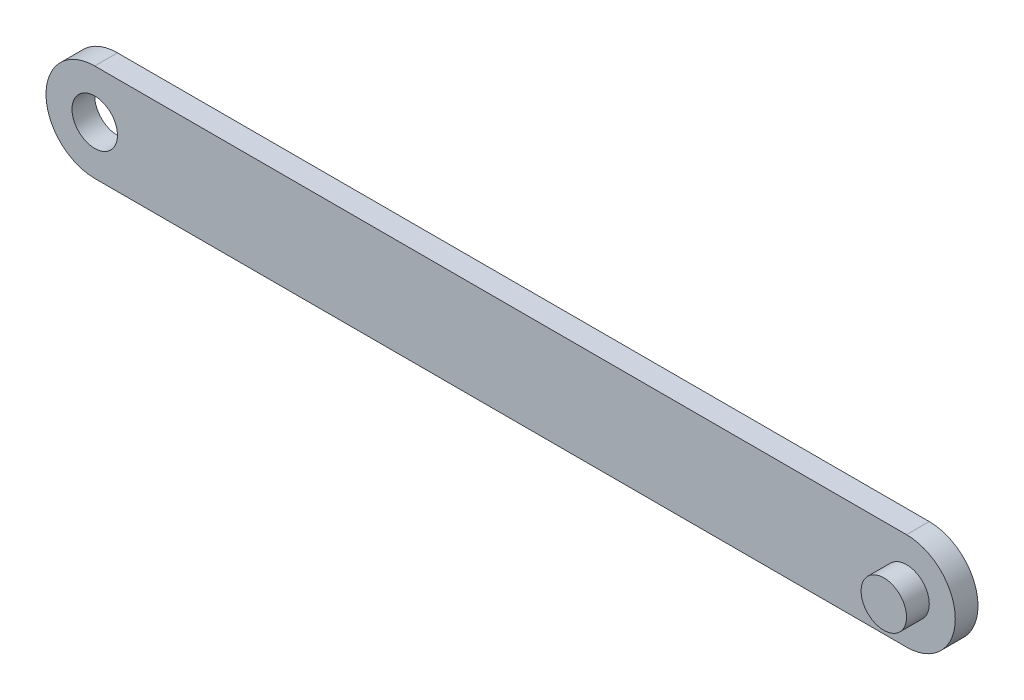
SolidWorks part; units mm, degrees
ref_plane "Front Plane" through (0, 0, 0) normal (0, 0, 1) x (1, 0, 0)
ref_plane "Top Plane" through (0, 0, 0) normal (0, 1, 0) x (1, 0, 0)
ref_plane "Right Plane" through (0, 0, 0) normal (1, 0, 0) x (0, 0, -1)
sketch "Sketch1" plane through (0, 0, 0) normal (0, 0, 1) x (1, 0, 0)
  line L0 (-813.7054, 0) -> (39871.5634, 0) construction
  line L1 (0, -813.7054) -> (0, 39871.5634) construction
  line L2 (-125, 0) -> (125, 0) construction
  line L3 (-125, 15) -> (125, 15)
  line L4 (-125, -15) -> (125, -15)
  arc A0 (-125, 15) -> (-125, -15) centre (-125, 0) ccw
  arc A1 (125, -15) -> (125, 15) centre (125, 0) ccw
  point P7 (0, 0)
  dimension "D1" = 30
  dimension "D2" = 250
extrude "Boss-Extrude1" add sketch "Sketch1" along normal blind 7
sketch "Sketch2" plane through (0, 0, 7) normal (0, 0, 1) x (1, 0, 0)
  line L0 (125, 15) -> (125, -15) construction
  circle A0 centre (125, 0) radius 7
  dimension "D1" = 14
extrude "Boss-Extrude2" add sketch "Sketch2" along normal blind 7
sketch "Sketch3" plane through (0, 0, 7) normal (0, 0, 1) x (1, 0, 0)
  line L0 (-125, 15) -> (-125, -15) construction
  arc A0 (-125, 15) -> (-125, -15) centre (-125, 0) ccw construction
  circle A1 centre (-125, 0) radius 7
  dimension "D1" = 14
extrude "Cut-Extrude1" cut sketch "Sketch3" against normal blind 7
